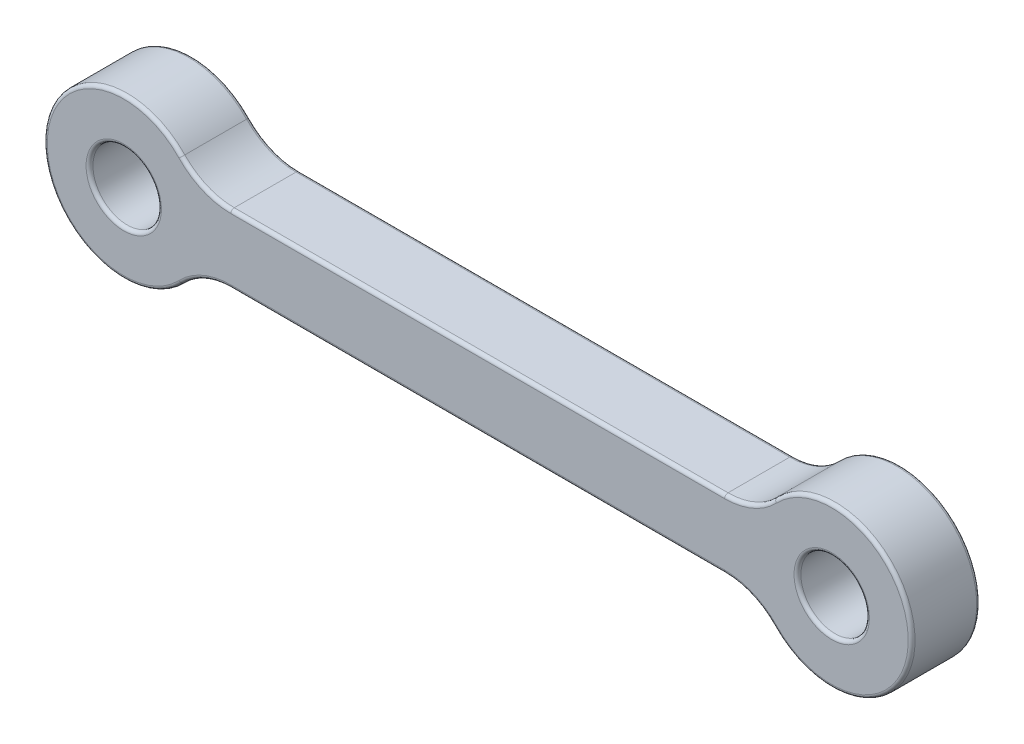
SolidWorks part; units mm, degrees
ref_plane "Front Plane" through (0, 0, 0) normal (0, 0, 1) x (1, 0, 0)
ref_plane "Top Plane" through (0, 0, 0) normal (0, 1, 0) x (1, 0, 0)
ref_plane "Right Plane" through (0, 0, 0) normal (1, 0, 0) x (0, 0, -1)
sketch "Sketch1" plane through (0, 0, 0) normal (0, 0, 1) x (1, 0, 0)
  line L0 (0, 0) -> (31, 0) construction
  line L1 (0, 3.5) -> (31, 3.5) construction
  line L2 (0, -3.5) -> (31, -3.5) construction
  line L3 (15.5, 0) -> (15.5, -3.5) construction
  line L5 (27.8377, -1.5) -> (3.1623, -1.5)
  line L6 (27.8377, -1.5) -> (27.8377, 1.5) construction
  line L7 (27.8377, 1.5) -> (3.1623, 1.5)
  line L8 (3.1623, -1.5) -> (3.1623, 1.5) construction
  line L9 (27.8377, -1.5) -> (3.1623, 1.5) construction
  line L10 (27.8377, 1.5) -> (3.1623, -1.5) construction
  arc A0 (0, 3.5) -> (0, -3.5) centre (0, 0) ccw construction
  arc A1 (31, -3.5) -> (31, 3.5) centre (31, 0) ccw construction
  circle A2 centre (0, 0) radius 3.5
  circle A3 centre (0, 0) radius 1.5
  circle A4 centre (31, 0) radius 1.5
  circle A5 centre (31, 0) radius 3.5
  point P3 (15.5, 0)
  dimension "D3" = 3
  dimension "D1" = 31
  dimension "D2" = 7
  dimension "D4" = 3
extrude "Boss-Extrude1" add sketch "Sketch1" along normal mid plane 3 contours A2 A3 | L5 A5 L7 A2 | A5 A4
fillet "Fillet1" radius 3 4 edges at (27.8377, -1.5, 0) (3.1623, -1.5, 0) (27.8377, 1.5, 0) (3.1623, 1.5, 0)
fillet "Fillet3" radius 0.15 20 edges at (32.5, 0, 1.5) (32.5, 0, -1.5) (1.5, 0, 1.5) (1.5, 0, -1.5) (3.5137, 1.7404, 1.5) (3.5137, 1.7404, -1.5) (-3.5, 0, -1.5) (-3.5, 0, 1.5) (3.5137, -1.7404, 1.5) (3.5137, -1.7404, -1.5) (15.5, -1.5, -1.5) (15.5, -1.5, 1.5) (27.4863, -1.7404, 1.5) (27.4863, -1.7404, -1.5) (34.5, 0, 1.5) (34.5, 0, -1.5) (27.4863, 1.7404, 1.5) (27.4863, 1.7404, -1.5) (15.5, 1.5, 1.5) (15.5, 1.5, -1.5)
